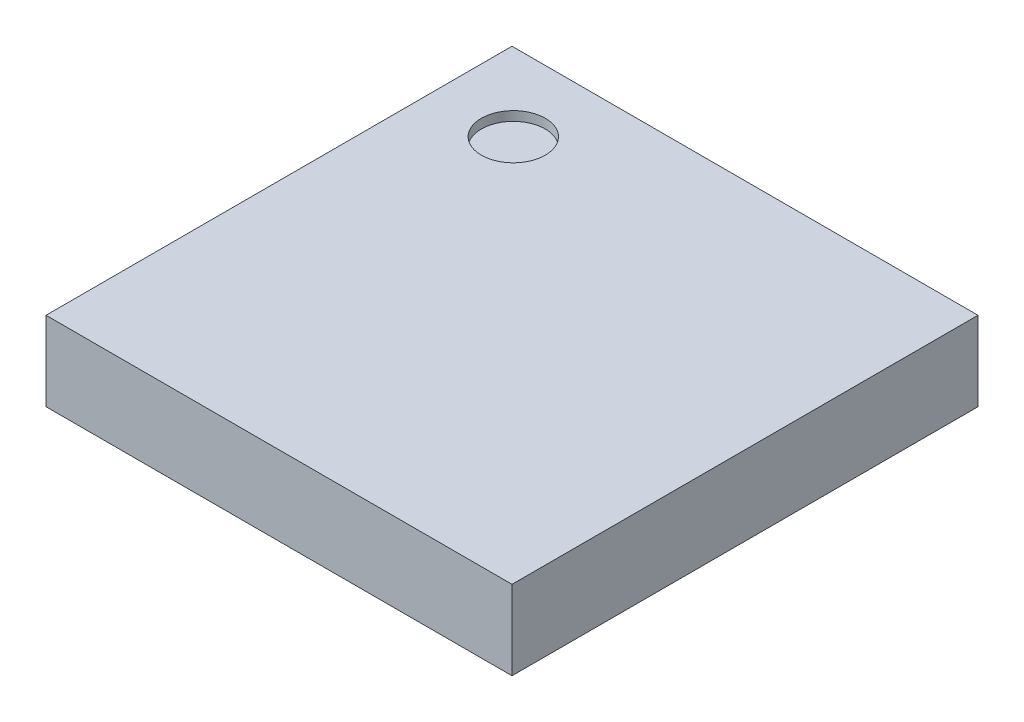
SolidWorks part; units mm, degrees
ref_plane "Front Plane" through (0, 0, 0) normal (0, 0, 1) x (1, 0, 0)
ref_plane "Top Plane" through (0, 0, 0) normal (0, 1, 0) x (1, 0, 0)
ref_plane "Right Plane" through (0, 0, 0) normal (1, 0, 0) x (0, 0, -1)
sketch "Sketch1" plane through (0, 0, 0) normal (0, 1, 0) x (1, 0, 0)
  line L1 (2.5, -2.5) -> (-2.5, -2.5)
  line L2 (2.5, -2.5) -> (2.5, 2.5)
  line L3 (2.5, 2.5) -> (-2.5, 2.5)
  line L4 (-2.5, -2.5) -> (-2.5, 2.5)
  line L5 (2.5, -2.5) -> (-2.5, 2.5) construction
  line L6 (2.5, 2.5) -> (-2.5, -2.5) construction
  point P0 (0, 0)
extrude "Boss-Extrude1" add sketch "Sketch1" along normal blind 0.85
sketch "Sketch2" plane through (0, 0.85, 0) normal (0, 1, 0) x (1, 0, 0)
  circle A0 centre (-1.6521, 1.6662) radius 0.3431
  point P2 (-1.6521, 1.6662)
extrude "Cut-Extrude1" cut sketch "Sketch2" against normal blind 0.1
